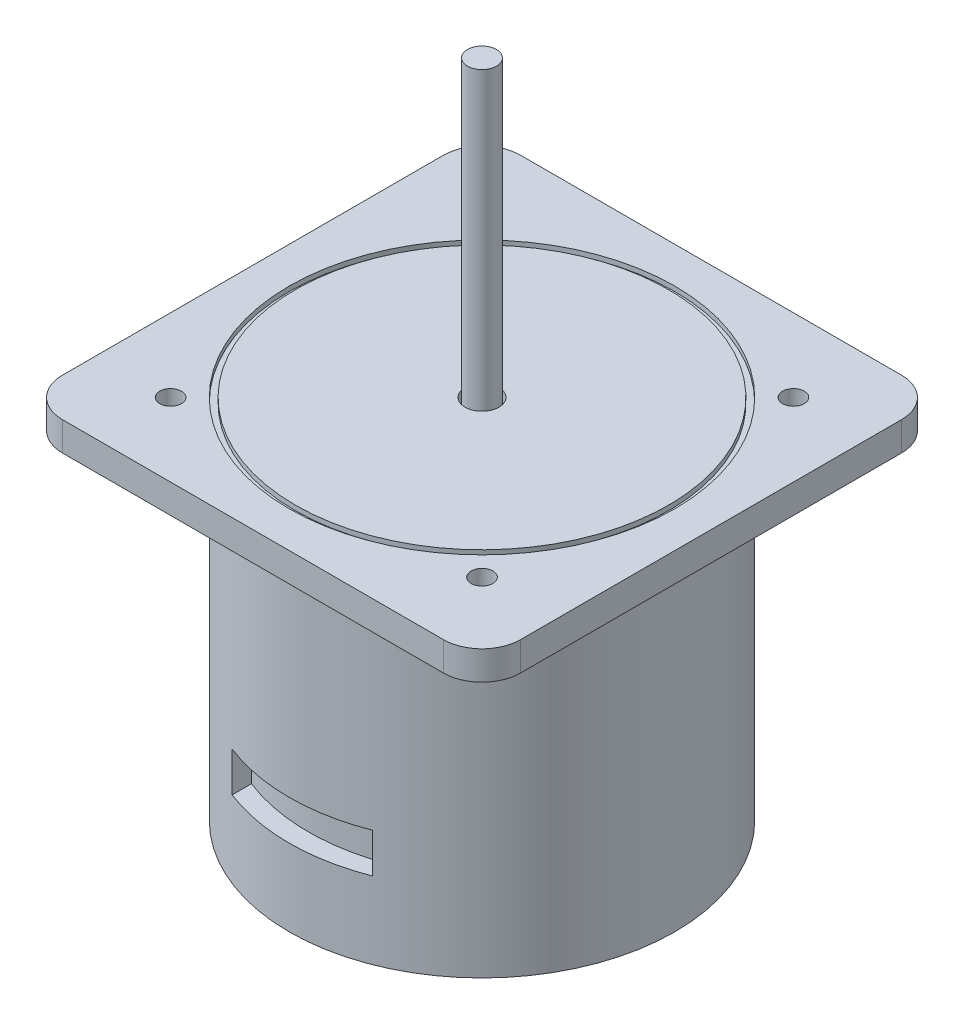
SolidWorks part; units mm, degrees
ref_plane "Front Plane" through (0, 0, 0) normal (0, 0, 1) x (1, 0, 0)
ref_plane "Top Plane" through (0, 0, 0) normal (0, 1, 0) x (1, 0, 0)
ref_plane "Right Plane" through (0, 0, 0) normal (1, 0, 0) x (0, 0, -1)
sketch "Sketch1" plane through (0, 0, 0) normal (0, 1, 0) x (1, 0, 0)
  circle A0 centre (0, 0) radius 40
  dimension "D1" = 80
extrude "Boss-Extrude1" add sketch "Sketch1" along normal blind 70
sketch "Sketch2" plane through (0, 70, 0) normal (0, 1, 0) x (1, 0, 0)
  line L1 (-47.5, 47.5) -> (47.5, 47.5)
  line L2 (-47.5, 47.5) -> (-47.5, -47.5)
  line L3 (-47.5, -47.5) -> (47.5, -47.5)
  line L4 (47.5, 47.5) -> (47.5, -47.5)
  line L5 (-47.5, 47.5) -> (47.5, -47.5) construction
  line L6 (-47.5, -47.5) -> (47.5, 47.5) construction
  point P0 (0, 0)
  dimension "D1" = 95
  dimension "D2" = 95
extrude "Boss-Extrude2" add sketch "Sketch2" along normal blind 6
sketch "Sketch3" plane through (0, 76, 0) normal (0, 1, 0) x (1, 0, 0)
  circle A0 centre (0, 0) radius 40
  circle A1 centre (0, 0) radius 38.7093
  dimension "D1" = 80
extrude "Cut-Extrude1" cut sketch "Sketch3" against normal blind 1
sketch "Sketch4" plane through (0, 76, 0) normal (0, 1, 0) x (1, 0, 0)
  circle A0 centre (0, 0) radius 3
  dimension "D1" = 6
extrude "Boss-Extrude3" add sketch "Sketch4" along normal blind 61 contours A0
sketch "Sketch5" plane through (0, 76, 0) normal (0, 1, 0) x (1, 0, 0)
  line L0 (41.1066, -41.1066) -> (47.5, -47.5) construction
  point P15 (0, 0)
fillet "Fillet1" radius 8 4 edges at (47.5, 73, 47.5) (-47.5, 73, 47.5) (-47.5, 73, -47.5) (47.5, 73, -47.5)
sketch "Sketch6" plane through (0, 76, 0) normal (0, 1, 0) x (1, 0, 0)
  circle A0 centre (0, 0) radius 3
  circle A1 centre (0, 0) radius 3.5196
extrude "Cut-Extrude3" cut sketch "Sketch6" against normal blind 5
sketch "Sketch8" plane through (0, 0, 0) normal (0, 0, 1) x (1, 0, 0)
  line L1 (-14.5736, 24.1663) -> (14.5736, 24.1663)
  line L2 (-14.5736, 24.1663) -> (-14.5736, 15.9453)
  line L3 (-14.5736, 15.9453) -> (14.5736, 15.9453)
  line L4 (14.5736, 24.1663) -> (14.5736, 15.9453)
  line L5 (-14.5736, 24.1663) -> (14.5736, 15.9453) construction
  line L6 (-14.5736, 15.9453) -> (14.5736, 24.1663) construction
  point P0 (0, 20.0558)
extrude "Cut-Extrude4" cut sketch "Sketch8" against normal blind 4 from surface starting at face at (0, 70, 40)
sketch "Sketch9" plane through (0, 0, 0) normal (0, -1, 0) x (1, 0, 0)
  line L0 (-25.7729, 4.2733) -> (-27.3191, 6.2899)
  line L1 (-25.6227, -4.3844) -> (-27.098, -6.4534)
  arc A0 (-25.6227, -4.3844) -> (-25.7729, 4.2733) centre (-22.4965, 0) cw
  arc A1 (-30.4224, 0) -> (-27.098, -6.4534) centre (-22.4965, 0) ccw
  arc A2 (-27.3191, 6.2899) -> (-27.098, -6.4534) centre (-22.4965, 0) ccw
extrude "Boss-Extrude5" add sketch "Sketch9" along normal blind 4 contours L0 A2 A1 L1 A0
mirror "Mirror1" about plane through (0, 0, 0) normal (1, 0, 0) of "Boss-Extrude5"
sketch "Sketch10" plane through (0, 76, 0) normal (0, 1, 0) x (1, 0, 0)
  line L0 (41.1066, -41.1066) -> (47.5, -47.5) construction
  circle A1 centre (-32.2956, 32.2956) radius 2.25
  circle A2 centre (32.2956, 32.2956) radius 2.25
  circle A3 centre (32.2956, -32.2956) radius 2.25
  circle A4 centre (-32.2956, -32.2956) radius 2.25
  point P16 (0, 0)
  dimension "D2" = 4.5
  dimension "D3" = 4
extrude "Cut-Extrude5" cut sketch "Sketch10" against normal blind 34
